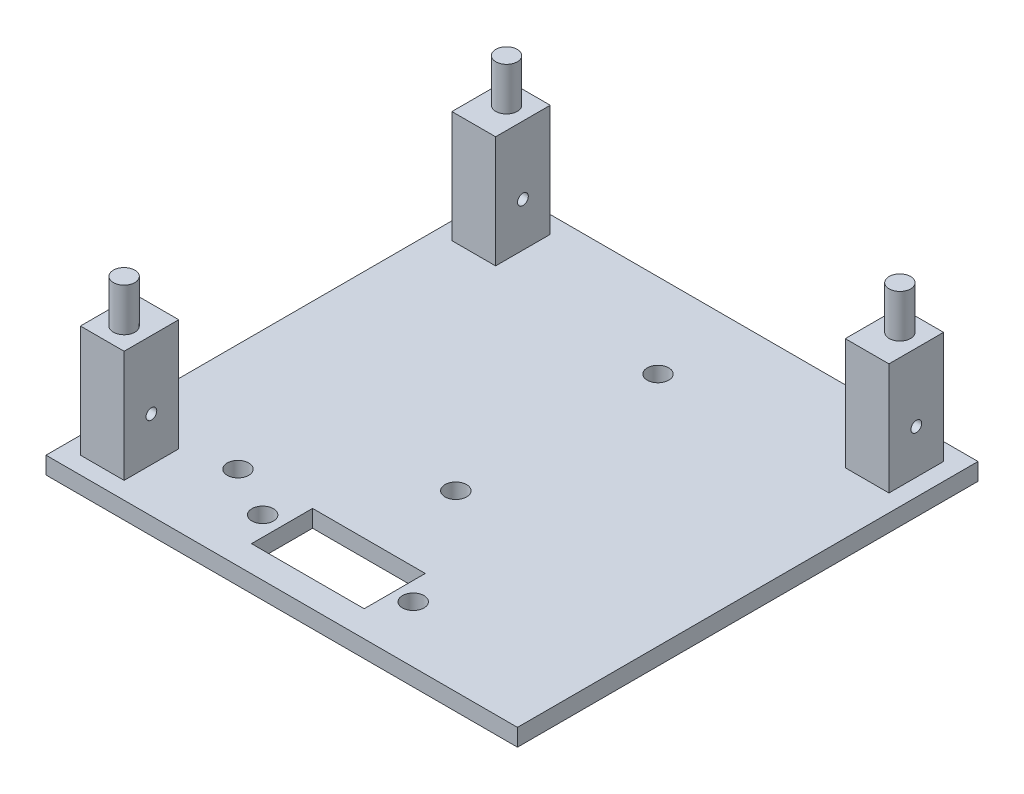
SolidWorks part; units mm, degrees
ref_plane "Front Plane" through (0, 0, 0) normal (0, 0, 1) x (1, 0, 0)
ref_plane "Top Plane" through (0, 0, 0) normal (0, 1, 0) x (1, 0, 0)
ref_plane "Right Plane" through (0, 0, 0) normal (1, 0, 0) x (0, 0, -1)
sketch "Sketch2" plane through (0, 0, 0) normal (0, 1, 0) x (1, 0, 0)
  line L1 (27.4, -26.765) -> (-27.4, -26.765)
  line L2 (27.4, -26.765) -> (27.4, 26.765)
  line L3 (27.4, 26.765) -> (-27.4, 26.765)
  line L4 (-27.4, -26.765) -> (-27.4, 26.765)
  line L5 (27.4, -26.765) -> (-27.4, 26.765) construction
  line L6 (27.4, 26.765) -> (-27.4, -26.765) construction
  point P0 (0, 0)
  dimension "D1" = 54.8
  dimension "D2" = 53.53
extrude "Boss-Extrude1" add sketch "Sketch2" along normal blind 2
sketch "Sketch3" plane through (0, 2, 0) normal (0, 1, 0) x (1, 0, 0)
  line L0 (27.4, 26.765) -> (-27.4, 26.765) construction
  line L1 (-20.32, 18.415) -> (-25.4, 18.415)
  line L2 (-20.32, 18.415) -> (-20.32, 24.765)
  line L3 (-20.32, 24.765) -> (-25.4, 24.765)
  line L4 (-25.4, 18.415) -> (-25.4, 24.765)
  line L5 (-20.32, 18.415) -> (-25.4, 24.765) construction
  line L6 (-20.32, 24.765) -> (-25.4, 18.415) construction
  line L7 (-27.4, 26.765) -> (-27.4, -26.765) construction
  line L8 (27.4, -26.765) -> (27.4, 26.765) construction
  line L9 (25.4, 18.415) -> (20.32, 18.415)
  line L10 (25.4, 18.415) -> (25.4, 24.765)
  line L11 (25.4, 24.765) -> (20.32, 24.765)
  line L12 (20.32, 18.415) -> (20.32, 24.765)
  line L13 (25.4, 18.415) -> (20.32, 24.765) construction
  line L14 (25.4, 24.765) -> (20.32, 18.415) construction
  line L15 (-27.4, -26.765) -> (27.4, -26.765) construction
  line L16 (-20.32, -24.765) -> (-25.4, -24.765)
  line L17 (-20.32, -24.765) -> (-20.32, -18.415)
  line L18 (-20.32, -18.415) -> (-25.4, -18.415)
  line L19 (-25.4, -24.765) -> (-25.4, -18.415)
  line L20 (-20.32, -24.765) -> (-25.4, -18.415) construction
  line L21 (-20.32, -18.415) -> (-25.4, -24.765) construction
  point P0 (-22.86, 21.59)
  point P7 (22.86, 21.59)
  point P16 (-22.86, -21.59)
  dimension "D1" = 2
  dimension "D2" = 2
  dimension "D3" = 5.08
  dimension "D4" = 6.35
  dimension "D5" = 5.08
  dimension "D6" = 6.35
  dimension "D7" = 2
  dimension "D8" = 2
  dimension "D9" = 2
  dimension "D10" = 2
  dimension "D11" = 5.08
  dimension "D12" = 6.35
extrude "Boss-Extrude2" add sketch "Sketch3" along normal blind 13
sketch "Sketch6" plane through (0, 15, 0) normal (0, 1, 0) x (1, 0, 0)
  line L0 (25.4, 24.765) -> (20.32, 24.765) construction
  line L2 (-20.32, 24.765) -> (-25.4, 24.765) construction
  line L3 (-25.4, 24.765) -> (-25.4, 18.415) construction
  line L4 (20.32, 24.765) -> (20.32, 18.415) construction
  line L6 (-20.32, -24.765) -> (-20.32, -18.415) construction
  line L8 (-25.4, -24.765) -> (-20.32, -24.765) construction
  circle A0 centre (-22.86, 22.225) radius 1.25
  circle A1 centre (22.86, 22.225) radius 1.25
  circle A2 centre (-22.86, -22.225) radius 1.25
  point P4 (-22.86, 24.765)
  point P17 (-22.86, -24.765)
  point P19 (22.86, 24.765)
  dimension "D1" = 2.54
  dimension "D3" = 2.54
  dimension "D5" = 2.54
  dimension "D2" = 2.54
  dimension "D4" = 2.54
  dimension "D6" = 2.54
extrude "Boss-Extrude3" add sketch "Sketch6" along normal blind 5
sketch "Sketch7" plane through (0, 0, 0) normal (0, -1, 0) x (-1, 0, 0)
  line L1 (6.55, -23.7306) -> (-6.55, -23.7306)
  line L2 (6.55, -23.7306) -> (6.55, -16.6306)
  line L3 (6.55, -16.6306) -> (-6.55, -16.6306)
  line L4 (-6.55, -23.7306) -> (-6.55, -16.6306)
  line L5 (6.55, -23.7306) -> (-6.55, -16.6306) construction
  line L6 (6.55, -16.6306) -> (-6.55, -23.7306) construction
  point P0 (0, -20.1806)
  dimension "D1" = 13.1
  dimension "D2" = 7.1
extrude "Cut-Extrude1" cut sketch "Sketch7" against normal up to next
sketch "Sketch8" plane through (0, 0, 0) normal (0, -1, 0) x (1, 0, 0)
  circle A0 centre (0, 6.5308) radius 1.25
  circle A1 centre (0, -16.9692) radius 1.25
  dimension "D1" = 23.5
extrude "Cut-Extrude2" cut sketch "Sketch8" against normal up to next
sketch "Sketch9" plane through (-25.4, 0, 0) normal (-1, 0, 0) x (0, 0, 1)
  circle A1 centre (-21.59, 7.1147) radius 0.625
extrude "Cut-Extrude4" cut sketch "Sketch9" against normal up to next
sketch "Sketch10" plane through (25.4, 0, 0) normal (1, 0, 0) x (0, 0, -1)
  line L0 (18.415, 15) -> (18.415, 2) construction
  line L1 (18.415, 2) -> (24.765, 2) construction
  circle A0 centre (21.595, 7.11) radius 0.625
  dimension "D1" = 3.18
  dimension "D2" = 5.11
extrude "Cut-Extrude5" cut sketch "Sketch10" against normal up to next
sketch "Sketch11" plane through (-25.4, 0, 0) normal (-1, 0, 0) x (0, 0, 1)
  line L0 (18.415, 15) -> (18.415, 2) construction
  line L6 (18.415, 2) -> (24.765, 2) construction
  circle A0 centre (21.595, 7.11) radius 0.625
  point P6 (21.5315, 2)
  point P7 (21.785, 2)
  point P8 (21.5731, 2)
  dimension "D1" = 3.18
  dimension "D2" = 5.11
extrude "Cut-Extrude6" cut sketch "Sketch11" against normal up to next
sketch "Sketch12" plane through (0, 2, 0) normal (0, 1, 0) x (1, 0, 0)
  circle A0 centre (-14.8355, -17.0172) radius 1.25
extrude "Cut-Extrude7" cut sketch "Sketch12" against normal up to next
sketch "Sketch13" plane through (0, 2, 0) normal (0, 1, 0) x (1, 0, 0)
  line L0 (-6.55, -23.7306) -> (-6.55, -16.6306) construction
  circle A0 centre (-8.8, -20.1806) radius 1.25
  circle A1 centre (8.7, -20.1806) radius 1.25
  point P2 (-6.55, -20.1806)
  dimension "D1" = 17.5
  dimension "D2" = 2.25
extrude "Cut-Extrude8" cut sketch "Sketch13" against normal up to next
